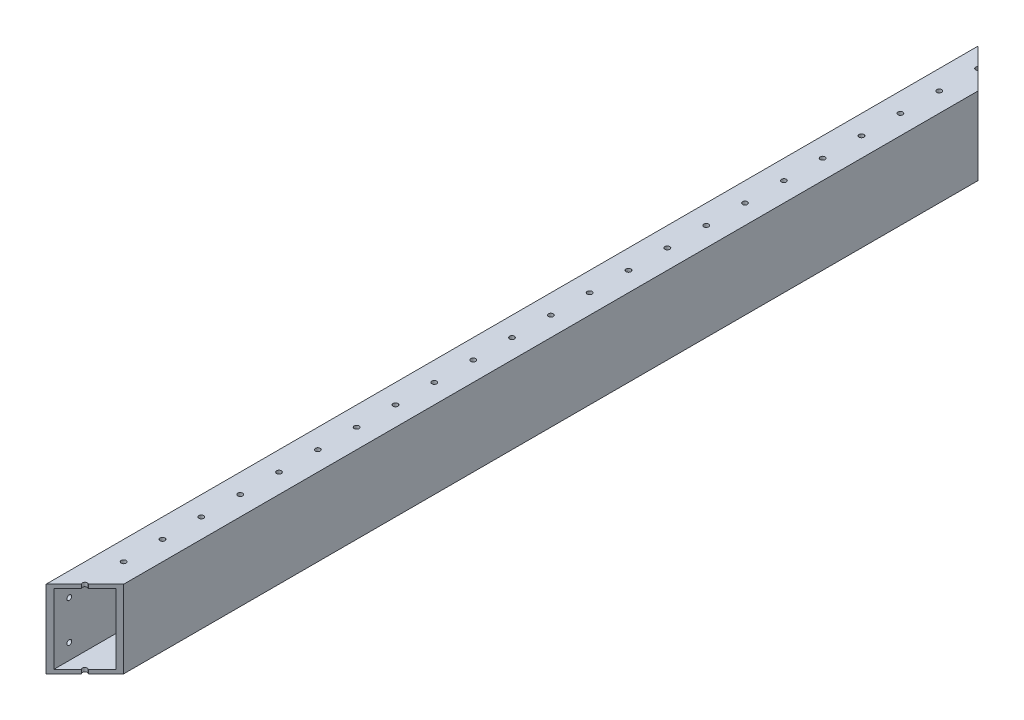
SolidWorks part; units mm, degrees
ref_plane "Front Plane" through (0, 0, 0) normal (0, 0, 1) x (1, 0, 0)
ref_plane "Top Plane" through (0, 0, 0) normal (0, 1, 0) x (1, 0, 0)
ref_plane "Right Plane" through (0, 0, 0) normal (1, 0, 0) x (0, 0, -1)
sketch "Sketch1" plane through (0, 0, 0) normal (0, 0, 1) x (1, 0, 0)
  line L1 (0, 0) -> (25.4, 0)
  line L2 (0, 0) -> (0, 50.8)
  line L3 (0, 50.8) -> (25.4, 50.8)
  line L4 (25.4, 0) -> (25.4, 50.8)
  dimension "D1" = 50.8
  dimension "D2" = 25.4
extrude "Extrude-Thin1" add sketch "Sketch1" along normal blind 609.6 thin thin type one direction reverse wall 2.54
sketch "Sketch2" plane through (0, 50.8, 0) normal (0, 1, 0) x (1, 0, 0)
  line L0 (12.7, -609.6) -> (12.7, -665.6007) construction
  line L1 (25.4, -609.6) -> (0, -609.6) construction
  circle A0 centre (12.7, -596.9) radius 1.5875
  dimension "D1" = 12.7
  dimension "D2" = 3.175
extrude "Cut-Extrude1" cut sketch "Sketch2" against normal through all
pattern_linear "LPattern1" count 50 spacing 25.4 along (0, 0, -1) of "Cut-Extrude1"
sketch "Sketch4" plane through (0, 50.8, 0) normal (0, 1, 0) x (1, 0, 0)
  line L0 (0, -609.6) -> (25.4, -584.2)
  line L1 (25.4, -609.6) -> (25.4, 0) construction
  line L2 (25.4, -584.2) -> (25.4, -609.6)
  line L3 (25.4, -609.6) -> (0, -609.6)
  line L4 (0, 0) -> (25.4, 0)
  line L5 (25.4, 0) -> (25.4, -25.4)
  line L6 (25.4, -25.4) -> (0, 0)
extrude "Cut-Extrude2" cut sketch "Sketch4" against normal through all
sketch "Sketch5" plane through (0, 0, 0) normal (-1, 0, 0) x (0, 0, 1)
  line L0 (304.8, 50.8) -> (304.8, 0) construction
  line L1 (609.6, 50.8) -> (0, 50.8) construction
  line L2 (609.6, 0) -> (0, 0) construction
  line L3 (12.7, 50.8) -> (12.7, 0) construction
  line L4 (584.2, 0) -> (25.4, 0) construction
  line L5 (0, 50.8) -> (0, 0) construction
  circle A0 centre (12.7, 12.7) radius 1.5875
  circle A1 centre (12.7, 38.1) radius 1.5875
  circle A2 centre (596.9, 38.1) radius 1.5875
  circle A3 centre (596.9, 12.7) radius 1.5875
  point P18 (11.5775, -10.1043)
  point P19 (27.8397, 0)
  point P24 (12.7, 31.7285)
  point P25 (0, 0)
  point P26 (0, 0)
  dimension "D1" = 3.175
  dimension "D3" = 25.4
  dimension "D2" = 12.7
  dimension "D4" = 12.7
extrude "Cut-Extrude3" cut sketch "Sketch5" against normal through all
